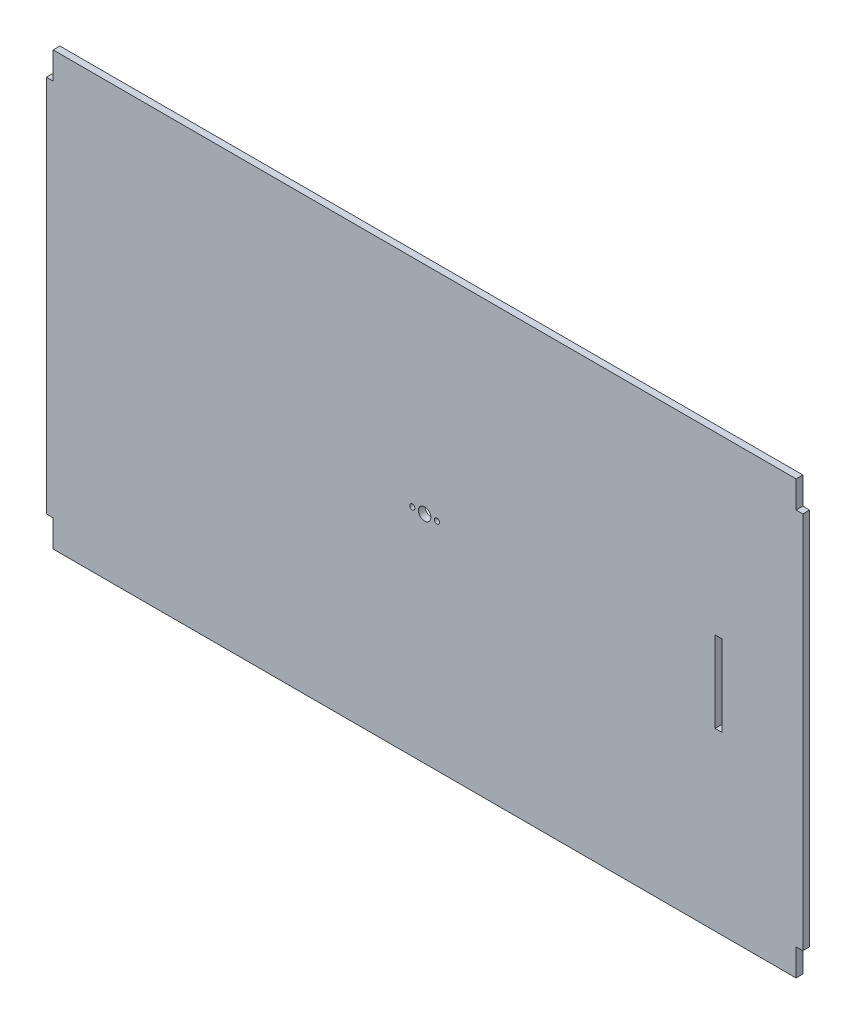
SolidWorks part; units mm, degrees
ref_plane "Front Plane" through (0, 0, 0) normal (0, 0, 1) x (1, 0, 0)
ref_plane "Top Plane" through (0, 0, 0) normal (0, 1, 0) x (1, 0, 0)
ref_plane "Right Plane" through (0, 0, 0) normal (1, 0, 0) x (0, 0, -1)
sketch "Sketch1" plane through (0, 0, 0) normal (0, 0, 1) x (1, 0, 0)
  line L0 (3.175, 203.2) -> (3.175, 190.5)
  line L1 (3.175, 0) -> (352.425, 0)
  line L2 (0, 12.7) -> (0, 190.5)
  line L3 (3.175, 203.2) -> (352.425, 203.2)
  line L4 (355.6, 12.7) -> (355.6, 190.5)
  line L5 (3.175, 190.5) -> (0, 190.5)
  line L6 (3.175, 12.7) -> (0, 12.7)
  line L7 (3.175, 12.7) -> (3.175, 0)
  line L8 (352.425, 0) -> (352.425, 12.7)
  line L9 (352.425, 12.7) -> (355.6, 12.7)
  line L10 (352.425, 203.2) -> (352.425, 190.5)
  line L11 (352.425, 190.5) -> (355.6, 190.5)
  dimension "D1" = 355.6
  dimension "D3" = 12.7
  dimension "D4" = 12.7
  dimension "D5" = 12.7
  dimension "D6" = 12.7
  dimension "D7" = 3.175
  dimension "D8" = 3.175
  dimension "D9" = 3.175
extrude "Shelf" add sketch "Sketch1" along normal blind 3.175
sketch "Tilt mount slot sketch" plane through (0, 0, 3.175) normal (0, 0, 1) x (1, 0, 0)
  line L1 (317.5, 120.65) -> (317.5, 203.2) construction
  line L2 (317.5, 120.65) -> (314.325, 120.65)
  line L3 (317.5, 120.65) -> (317.5, 82.55)
  line L4 (317.5, 82.55) -> (314.325, 82.55)
  line L5 (314.325, 120.65) -> (314.325, 82.55)
  line L6 (352.425, 203.2) -> (3.175, 203.2) construction
  line L7 (317.5, 82.55) -> (317.5, 0) construction
  line L8 (3.175, 0) -> (352.425, 0) construction
  line L9 (355.6, 12.7) -> (355.6, 190.5) construction
  dimension "D1" = 3.175
  dimension "D2" = 38.1
  dimension "D3" = 38.1
extrude "Tilt Mount Slot" cut sketch "Tilt mount slot sketch" against normal through all
sketch "Sketch2" plane through (0, 0, 3.175) normal (0, 0, 1) x (1, 0, 0)
  line L0 (355.6, 101.6) -> (0, 101.6) construction
  line L1 (355.6, 12.7) -> (355.6, 190.5) construction
  line L2 (0, 190.5) -> (0, 12.7) construction
  line L3 (177.8, 203.2) -> (177.8, 0) construction
  line L4 (352.425, 203.2) -> (3.175, 203.2) construction
  line L5 (3.175, 0) -> (352.425, 0) construction
  circle A0 centre (177.8, 101.6) radius 2.921
  circle A1 centre (183.5785, 101.6) radius 1.2065
  circle A2 centre (172.0215, 101.6) radius 1.2065
  dimension "D1" = 2.413
  dimension "D2" = 5.842
  dimension "D3" = 5.7785
  dimension "D4" = 5.7785
extrude "Cut-Extrude1" cut sketch "Sketch2" against normal through all
